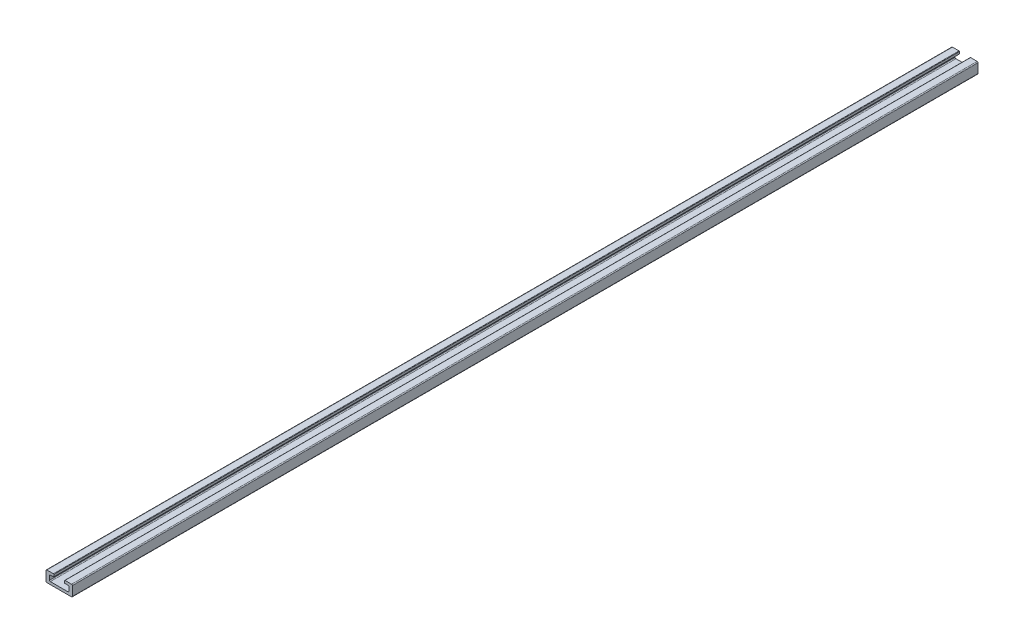
SolidWorks part; units mm, degrees
ref_plane "前视基准面" through (0, 0, 0) normal (0, 0, 1) x (1, 0, 0)
ref_plane "上视基准面" through (0, 0, 0) normal (0, 1, 0) x (1, 0, 0)
ref_plane "右视基准面" through (0, 0, 0) normal (1, 0, 0) x (0, 0, -1)
other "Configuration Table"
ref_plane "基准面1" through (0, 0, -515) normal (0, 0, -1) x (-1, 0, 0)
sketch "草图1" plane through (0, 0, -515) normal (0, 0, -1) x (-1, 0, 0)
  line L0 (15, -5.25) -> (15, 5.25)
  line L1 (14, 6.25) -> (6.6, 6.25)
  line L2 (6.1, 5.75) -> (6.1, 3.45)
  line L3 (6.3, 3.25) -> (10, 3.25)
  line L4 (11, 2.25) -> (11, -2.25)
  line L5 (10, -3.25) -> (-10, -3.25)
  line L6 (-11, -2.25) -> (-11, 2.25)
  line L7 (-10, 3.25) -> (-6.3, 3.25)
  line L8 (-6.1, 3.45) -> (-6.1, 5.75)
  line L9 (-6.6, 6.25) -> (-14, 6.25)
  line L10 (-15, 5.25) -> (-15, -5.25)
  line L11 (-14, -6.25) -> (14, -6.25)
  arc A0 (15, 5.25) -> (14, 6.25) centre (14, 5.25) ccw
  arc A1 (6.6, 6.25) -> (6.1, 5.75) centre (6.6, 5.75) ccw
  arc A2 (6.1, 3.45) -> (6.3, 3.25) centre (6.3, 3.45) ccw
  arc A3 (10, 3.25) -> (11, 2.25) centre (10, 2.25) cw
  arc A4 (11, -2.25) -> (10, -3.25) centre (10, -2.25) cw
  arc A5 (-10, -3.25) -> (-11, -2.25) centre (-10, -2.25) cw
  arc A6 (-11, 2.25) -> (-10, 3.25) centre (-10, 2.25) cw
  arc A7 (-6.3, 3.25) -> (-6.1, 3.45) centre (-6.3, 3.45) ccw
  arc A8 (-6.1, 5.75) -> (-6.6, 6.25) centre (-6.6, 5.75) ccw
  arc A9 (-14, 6.25) -> (-15, 5.25) centre (-14, 5.25) ccw
  arc A10 (-15, -5.25) -> (-14, -6.25) centre (-14, -5.25) ccw
  arc A11 (14, -6.25) -> (15, -5.25) centre (14, -5.25) ccw
extrude "凸台-拉伸1" add sketch "草图1" against normal blind 1030
hole_wizard "M3 六角头机械螺钉的柱形沉头孔1" positions "草图3" profile "草图2" counterbore size "M3" standard "ANSI Metric"
sketch "草图3" plane through (0, -3.25, 0) normal (0, 1, 0) x (1, 0, 0)
  point P0 (0, -500)
  point P1 (0, -460)
  point P2 (0, -420)
  point P3 (0, -380)
  point P4 (0, -340)
  point P5 (0, -300)
  point P6 (0, -260)
  point P7 (0, -220)
  point P8 (0, -180)
  point P9 (0, -140)
  point P10 (0, 20)
  point P11 (0, 60)
  point P12 (0, 100)
  point P13 (0, 140)
  point P14 (0, 180)
  point P15 (0, 220)
  point P16 (0, 260)
  point P17 (0, 300)
  point P18 (0, 340)
  point P19 (0, 380)
  point P20 (0, 420)
  point P21 (0, 460)
  point P22 (0, 500)
  point P23 (0, -100)
  point P24 (0, -60)
  point P25 (0, -20)
sketch "草图2" plane through (0, -3.25, 500) normal (1, 0, 0) x (0, 0, 1)
  line L0 (0, 0) -> (0, 3)
  line L1 (0, 3) -> (1.75, 3)
  line L3 (1.75, 3) -> (1.75, 2)
  line L4 (1.75, 2) -> (3, 2)
  line L5 (3, 2) -> (3, 0)
  line L7 (3, 0) -> (0, 0)
  line L11 (0, -6.35) -> (0, 107.95) construction
  dimension "通孔孔直径" = 3.5
  dimension "通孔孔深度" = 3
  dimension "柱形沉头孔直径" = 6
  dimension "柱形沉头孔深度" = 2
